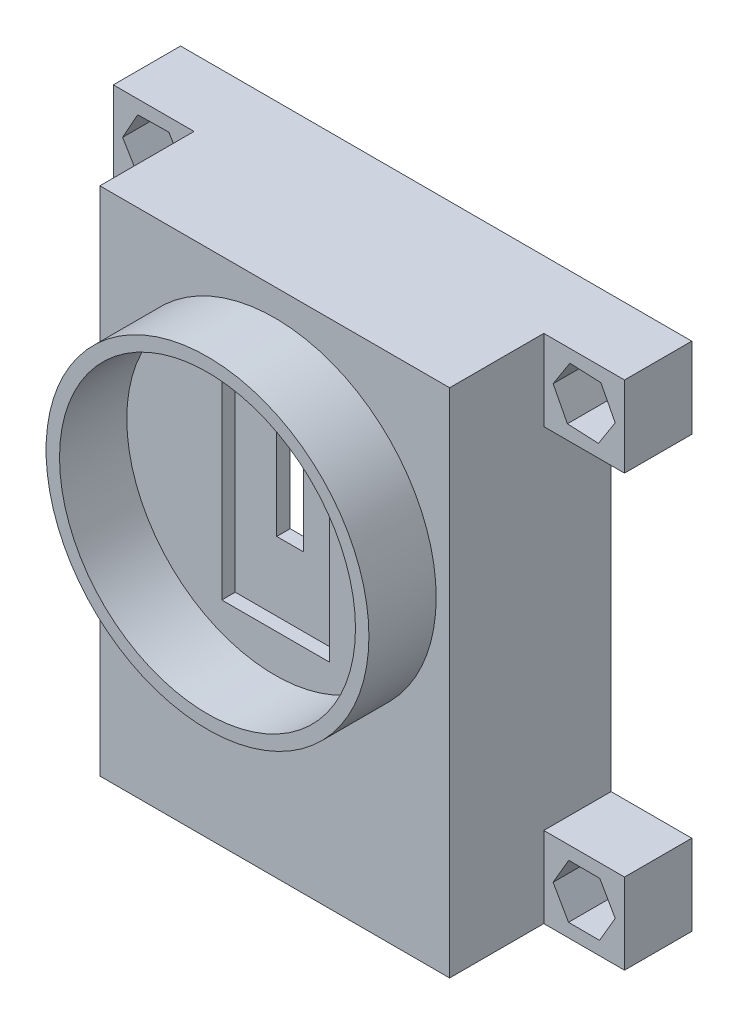
SolidWorks part; units mm, degrees
ref_plane "正面" through (0, 0, 0) normal (0, 0, 1) x (1, 0, 0)
ref_plane "平面" through (0, 0, 0) normal (0, 1, 0) x (1, 0, 0)
ref_plane "右側面" through (0, 0, 0) normal (1, 0, 0) x (0, 0, -1)
sketch "ｽｹｯﾁ1" plane through (0, 0, 0) normal (0, 0, 1) x (1, 0, 0)
  line L1 (13, -19) -> (-13, -19)
  line L2 (13, -19) -> (13, 19)
  line L3 (13, 19) -> (-13, 19)
  line L4 (-13, -19) -> (-13, 19)
  line L5 (13, -19) -> (-13, 19) construction
  line L6 (13, 19) -> (-13, -19) construction
  point P0 (0, 0)
  dimension "D1" = 38
  dimension "D2" = 26
extrude "ﾎﾞｽ - 押し出し1" add sketch "ｽｹｯﾁ1" along normal blind 12
sketch "ｽｹｯﾁ2" plane through (0, 0, 0) normal (0, 0, 1) x (1, 0, 0)
  line L1 (11, -17) -> (-11, -17)
  line L2 (11, -17) -> (11, 17)
  line L3 (11, 17) -> (-11, 17)
  line L4 (-11, -17) -> (-11, 17)
  line L5 (11, -17) -> (-11, 17) construction
  line L6 (11, 17) -> (-11, -17) construction
  point P0 (0, 0)
  dimension "D1" = 22
  dimension "D2" = 34
extrude "ｶｯﾄ - 押し出し1" cut sketch "ｽｹｯﾁ2" along normal blind 10
sketch "ｽｹｯﾁ3" plane through (0, 0, 0) normal (0, 0, 1) x (1, 0, 0)
  line L0 (13, 19) -> (-13, 19) construction
  line L1 (-0.8522, 2) -> (1.1478, 2)
  line L2 (-0.8522, 2) -> (-0.8522, 9)
  line L3 (-0.8522, 9) -> (1.1478, 9)
  line L4 (1.1478, 2) -> (1.1478, 9)
  line L5 (-0.8522, 2) -> (1.1478, 9) construction
  line L6 (-0.8522, 9) -> (1.1478, 2) construction
  point P0 (0.1478, 5.5)
  dimension "D1" = 7
  dimension "D2" = 2
  dimension "D3" = 10
extrude "ｶｯﾄ - 押し出し3" cut sketch "ｽｹｯﾁ3" along normal blind 12
sketch "ｽｹｯﾁ4" plane through (0, 0, 0) normal (0, 0, 1) x (1, 0, 0)
  line L0 (13, -19) -> (13, 19) construction
  line L1 (13, 19) -> (19, 19)
  line L2 (13, 19) -> (13, 13)
  line L3 (13, 13) -> (19, 13)
  line L4 (19, 19) -> (19, 13)
  line L5 (13, -19) -> (19, -19)
  line L6 (13, -19) -> (13, -13)
  line L7 (13, -13) -> (19, -13)
  line L8 (19, -19) -> (19, -13)
  line L9 (-13, -19) -> (13, -19) construction
  line L10 (-13, -19) -> (-19, -19)
  line L11 (-13, -19) -> (-13, -13)
  line L12 (-13, -13) -> (-19, -13)
  line L13 (-19, -19) -> (-19, -13)
  line L14 (-13, 19) -> (-19, 19)
  line L15 (-13, 19) -> (-13, 13)
  line L16 (-13, 13) -> (-19, 13)
  line L17 (-19, 19) -> (-19, 13)
  dimension "D1" = 6
  dimension "D2" = 6
  dimension "D3" = 6
  dimension "D4" = 6
  dimension "D5" = 6
  dimension "D6" = 6
  dimension "D7" = 6
  dimension "D8" = 6
  dimension "D9" = 6
extrude "ﾎﾞｽ - 押し出し2" add sketch "ｽｹｯﾁ4" along normal blind 5
sketch "ｽｹｯﾁ5" plane through (0, 0, 0) normal (0, 0, 1) x (1, 0, 0)
  line L0 (-13, 19) -> (-19, 19) construction
  line L1 (-19, 19) -> (-19, 13) construction
  line L2 (-13, -13) -> (-19, -13) construction
  line L3 (19, -19) -> (19, -13) construction
  line L5 (13, 13) -> (19, 13) construction
  line L7 (19, -13) -> (13, -13) construction
  circle A0 centre (-16, 16) radius 1
  circle A1 centre (-16, -16) radius 1
  circle A2 centre (16, -16) radius 1
  circle A3 centre (16, 16) radius 1
  point P16 (16, 13)
  dimension "D1" = 3
  dimension "D2" = 3
  dimension "D3" = 3
  dimension "D4" = 2
  dimension "D5" = 2
  dimension "D6" = 3
  dimension "D7" = 2
  dimension "D8" = 2
  dimension "D9" = 3
  dimension "D10" = 3
extrude "ｶｯﾄ - 押し出し4" cut sketch "ｽｹｯﾁ5" along normal through all
sketch "ｽｹｯﾁ6" plane through (0, 0, 0) normal (0, 0, 1) x (1, 0, 0)
  line L0 (-19, 19) -> (-19, 13) construction
  line L1 (-17.1841, 17.9827) -> (-18.3091, 15.9659)
  line L2 (-18.3091, 15.9659) -> (-17.125, 13.9832)
  line L3 (-17.125, 13.9832) -> (-14.8159, 14.0173)
  line L4 (-14.8159, 14.0173) -> (-13.6909, 16.0341)
  line L5 (-13.6909, 16.0341) -> (-14.875, 18.0168)
  line L6 (-14.875, 18.0168) -> (-17.1841, 17.9827)
  line L7 (-19, -19) -> (-13, -19) construction
  line L8 (-17.0756, -13.9564) -> (-18.3076, -15.9097)
  line L9 (-18.3076, -15.9097) -> (-17.232, -17.9533)
  line L10 (-17.232, -17.9533) -> (-14.9244, -18.0436)
  line L11 (-14.9244, -18.0436) -> (-13.6924, -16.0903)
  line L12 (-13.6924, -16.0903) -> (-14.768, -14.0467)
  line L13 (-14.768, -14.0467) -> (-17.0756, -13.9564)
  line L14 (-13, 19) -> (-19, 19) construction
  line L15 (19, 19) -> (13, 19) construction
  line L16 (14.9393, 18.0514) -> (13.6931, 16.1072)
  line L17 (13.6931, 16.1072) -> (14.7537, 14.0557)
  line L18 (14.7537, 14.0557) -> (17.0607, 13.9486)
  line L19 (17.0607, 13.9486) -> (18.3069, 15.8928)
  line L20 (18.3069, 15.8928) -> (17.2463, 17.9443)
  line L21 (17.2463, 17.9443) -> (14.9393, 18.0514)
  line L22 (19, 13) -> (19, 19) construction
  line L23 (19, -19) -> (19, -13) construction
  line L24 (14.8545, -13.9947) -> (13.6906, -15.9894)
  line L25 (13.6906, -15.9894) -> (14.8362, -17.9947)
  line L26 (14.8362, -17.9947) -> (17.1455, -18.0053)
  line L27 (17.1455, -18.0053) -> (18.3094, -16.0106)
  line L28 (18.3094, -16.0106) -> (17.1638, -14.0053)
  line L29 (17.1638, -14.0053) -> (14.8545, -13.9947)
  line L30 (19, -13) -> (13, -13) construction
  line L31 (-19, -13) -> (-19, -19) construction
  circle A0 centre (-16, 16) radius 2 construction
  circle A1 centre (-16, -16) radius 2 construction
  circle A2 centre (16, 16) radius 2 construction
  circle A3 centre (16, -16) radius 2 construction
  point P23 (16, 19)
  point P45 (16, -13)
  dimension "D1" = 4
  dimension "D3" = 4
  dimension "D6" = 4
  dimension "D9" = 4
  dimension "D2" = 3
  dimension "D4" = 3
  dimension "D5" = 3
  dimension "D7" = 3
  dimension "D8" = 3
  dimension "D10" = 3
  dimension "D11" = 3
  dimension "D12" = 3
extrude "ｶｯﾄ - 押し出し5" cut sketch "ｽｹｯﾁ6" along normal blind 4 from offset 1
sketch "ｽｹｯﾁ7" plane through (0, 0, 12) normal (0, 0, 1) x (1, 0, 0)
  line L0 (-13, 19) -> (-13, -19) construction
  line L1 (13, 19) -> (-13, 19) construction
  circle A0 centre (0, 5) radius 12
  circle A1 centre (0, 5) radius 11
  dimension "D1" = 24
  dimension "D4" = 22
  dimension "D2" = 13
  dimension "D3" = 14
extrude "ﾎﾞｽ - 押し出し3" add sketch "ｽｹｯﾁ7" along normal blind 5
sketch "ｽｹｯﾁ8" plane through (0, 0, 0) normal (1, 0, 0) x (0, 0, -1)
  line L0 (-17, 17) -> (-17, -7) construction
  circle A0 centre (-14, 5.2266) radius 1
  dimension "D1" = 2
  dimension "D2" = 3
extrude "ｶｯﾄ - 押し出し6" [suppressed] cut sketch "ｽｹｯﾁ8" against normal blind 20
pattern_linear "直線ﾊﾟﾀｰﾝ1" [suppressed] count 2 spacing 5
pattern_circular "円形ﾊﾟﾀｰﾝ1" [suppressed] count 12 over 360
sketch "ｽｹｯﾁ9" plane through (0, 0, 12) normal (0, 0, 1) x (1, 0, 0)
  line L1 (4.0613, -3.1328) -> (-3.9387, -3.1328)
  line L2 (4.0613, -3.1328) -> (4.0613, 11.8672)
  line L3 (4.0613, 11.8672) -> (-3.9387, 11.8672)
  line L4 (-3.9387, -3.1328) -> (-3.9387, 11.8672)
  line L5 (4.0613, -3.1328) -> (-3.9387, 11.8672) construction
  line L6 (4.0613, 11.8672) -> (-3.9387, -3.1328) construction
  point P0 (0.0613, 4.3672)
  dimension "D1" = 8
  dimension "D2" = 15
extrude "ｶｯﾄ - 押し出し7" cut sketch "ｽｹｯﾁ9" against normal blind 1
sketch "ｽｹｯﾁ10" plane through (0, 0, 10) normal (0, 0, 1) x (1, 0, 0)
  line L1 (-7.2055, -13) -> (7.2055, -13)
  line L2 (-7.2055, -13) -> (-7.2055, -10)
  line L3 (-7.2055, -10) -> (7.2055, -10)
  line L4 (7.2055, -13) -> (7.2055, -10)
  line L5 (-7.2055, -13) -> (7.2055, -10) construction
  line L6 (-7.2055, -10) -> (7.2055, -13) construction
  point P0 (0, -11.5)
  dimension "D1" = 3
  dimension "D2" = 10
extrude "ﾎﾞｽ - 押し出し4" add sketch "ｽｹｯﾁ10" against normal blind 2
